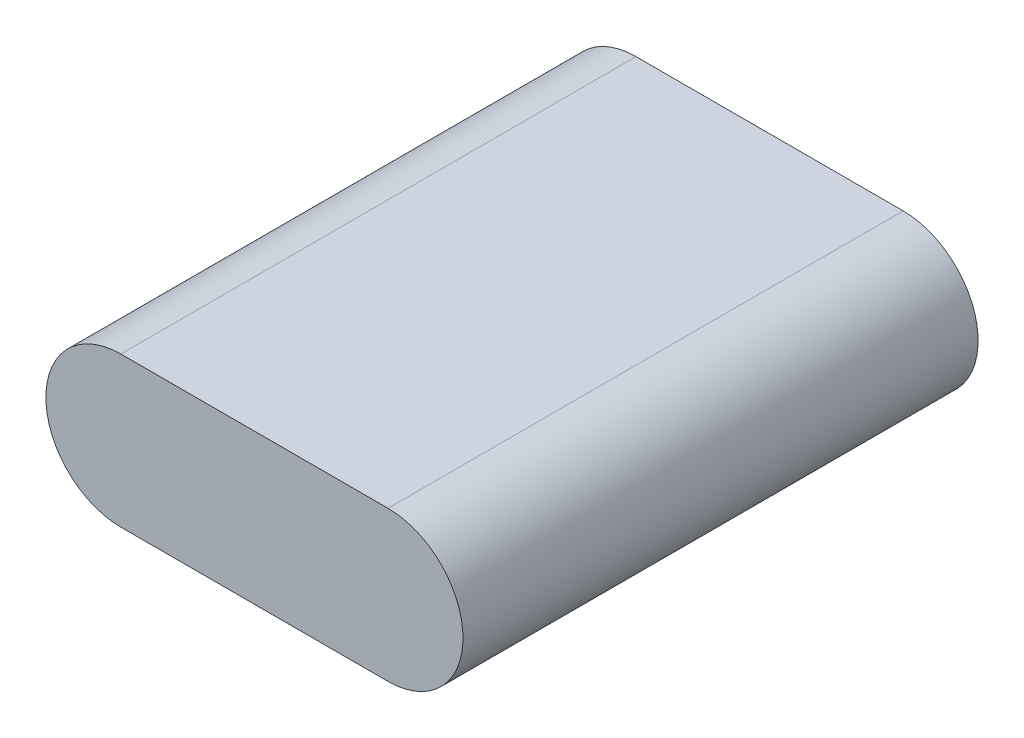
SolidWorks part; units mm, degrees
ref_plane "Front Plane" through (0, 0, 0) normal (0, 0, 1) x (1, 0, 0)
ref_plane "Top Plane" through (0, 0, 0) normal (0, 1, 0) x (1, 0, 0)
ref_plane "Right Plane" through (0, 0, 0) normal (1, 0, 0) x (0, 0, -1)
sketch "Sketch3" plane through (0, 0, 0) normal (0, 0, 1) x (1, 0, 0)
  line L0 (-17.653, 0) -> (17.653, 0) construction
  line L1 (-17.653, 9.906) -> (17.653, 9.906)
  line L2 (-17.653, -9.906) -> (17.653, -9.906)
  arc A0 (-17.653, 9.906) -> (-17.653, -9.906) centre (-17.653, 0) ccw
  arc A1 (17.653, -9.906) -> (17.653, 9.906) centre (17.653, 0) ccw
  point P3 (0, 0)
  point P8 (0, 0)
  dimension "D1" = 9.906
  dimension "D2" = 35.306
extrude "Boss-Extrude1" add sketch "Sketch3" along normal blind 68.072
